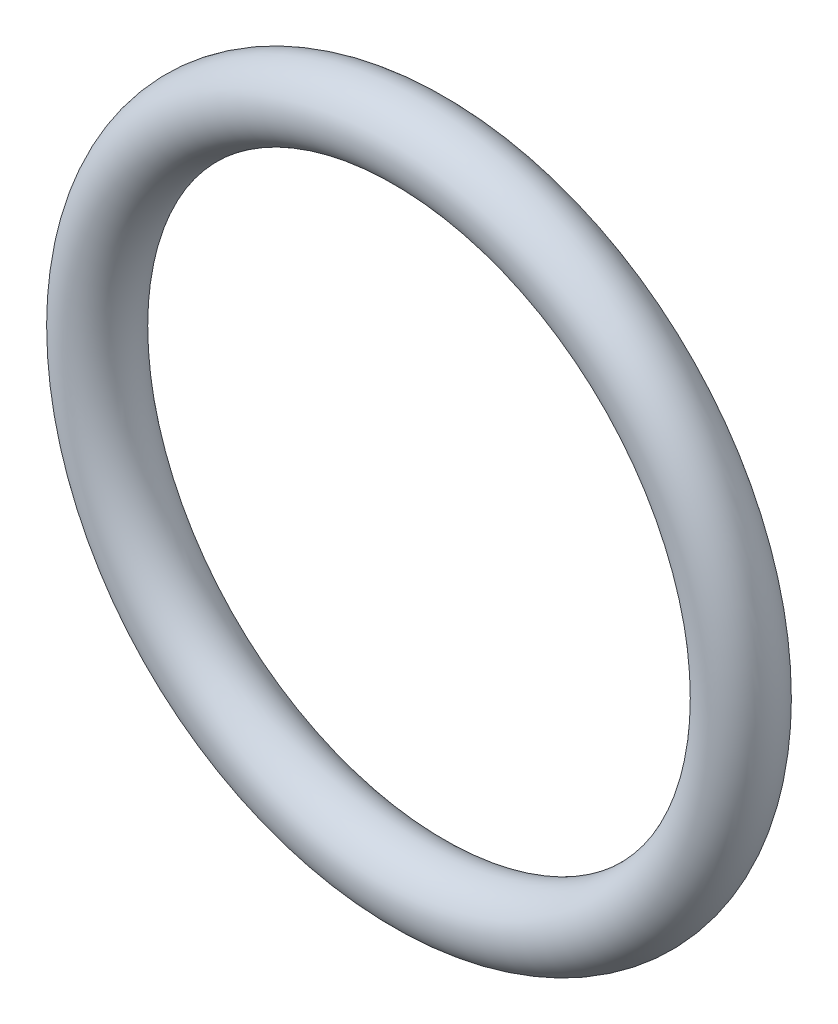
SolidWorks part; units mm, degrees
ref_plane "Front" through (0, 0, 0) normal (0, 0, 1) x (1, 0, 0)
ref_plane "Top" through (0, 0, 0) normal (0, 1, 0) x (1, 0, 0)
ref_plane "Right" through (0, 0, 0) normal (1, 0, 0) x (0, 0, -1)
sketch "Sketch1" plane through (0, 0, 0) normal (1, 0, 0) x (0, -1, 0)
  line L0 (0, -0.5) -> (0, 0.5) construction
  line L2 (-5.775, 0) -> (5.775, 0) construction
  line L3 (-4, 0) -> (4, 0) construction
  circle A0 centre (4.5, 0) radius 0.5
  point P9 (4, 0)
  point P10 (5, 0)
  point P13 (4.5, 0.5)
  point P14 (4.5, -0.5)
  dimension "Width" = 1
  dimension "ID" = 8
revolve "Revolve1" add sketch "Sketch1" angle 360 about L0
sketch "Sketch2" plane through (0, 0, 0) normal (0, 0, 1) x (1, 0, 0)
  circle A0 centre (0, 0) radius 4
  dimension "D1" = 8
